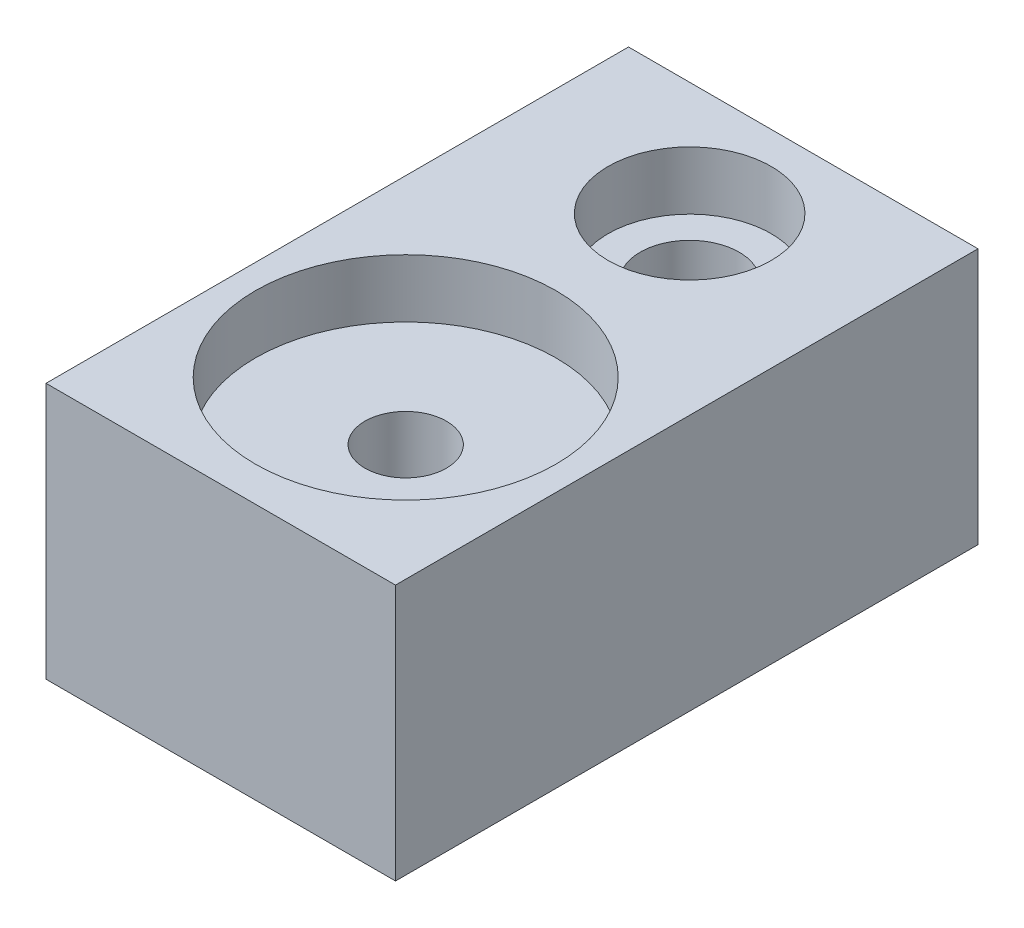
SolidWorks part; units mm, degrees
ref_plane "前视基准面" through (0, 0, 0) normal (0, 0, 1) x (1, 0, 0)
ref_plane "上视基准面" through (0, 0, 0) normal (0, 1, 0) x (1, 0, 0)
ref_plane "右视基准面" through (0, 0, 0) normal (1, 0, 0) x (0, 0, -1)
other "Configuration Table"
sketch "草图1" plane through (0, 0, 0) normal (0, 1, 0) x (1, 0, 0)
  line L1 (-15, 25) -> (15, 25)
  line L2 (-15, 25) -> (-15, -25)
  line L3 (-15, -25) -> (15, -25)
  line L4 (15, 25) -> (15, -25)
  circle A1 centre (0, -9.125) radius 3.5
  circle A2 centre (0, 15.25) radius 4.25
extrude "凸台-拉伸1" add sketch "草图1" along normal blind 22
sketch "草图2" plane through (0, 22, 0) normal (0, 1, 0) x (1, 0, 0)
  circle A0 centre (0, -9.125) radius 12.9
extrude "切除-拉伸1" cut sketch "草图2" against normal blind 5
sketch "草图3" plane through (0, 0, 0) normal (0, -1, 0) x (1, 0, 0)
  circle A0 centre (0, 9.125) radius 6
extrude "切除-拉伸2" cut sketch "草图3" against normal blind 3.5
sketch "草图4" plane through (0, 22, 0) normal (0, 1, 0) x (1, 0, 0)
  circle A0 centre (0, 15.25) radius 7
extrude "切除-拉伸3" cut sketch "草图4" against normal blind 5
